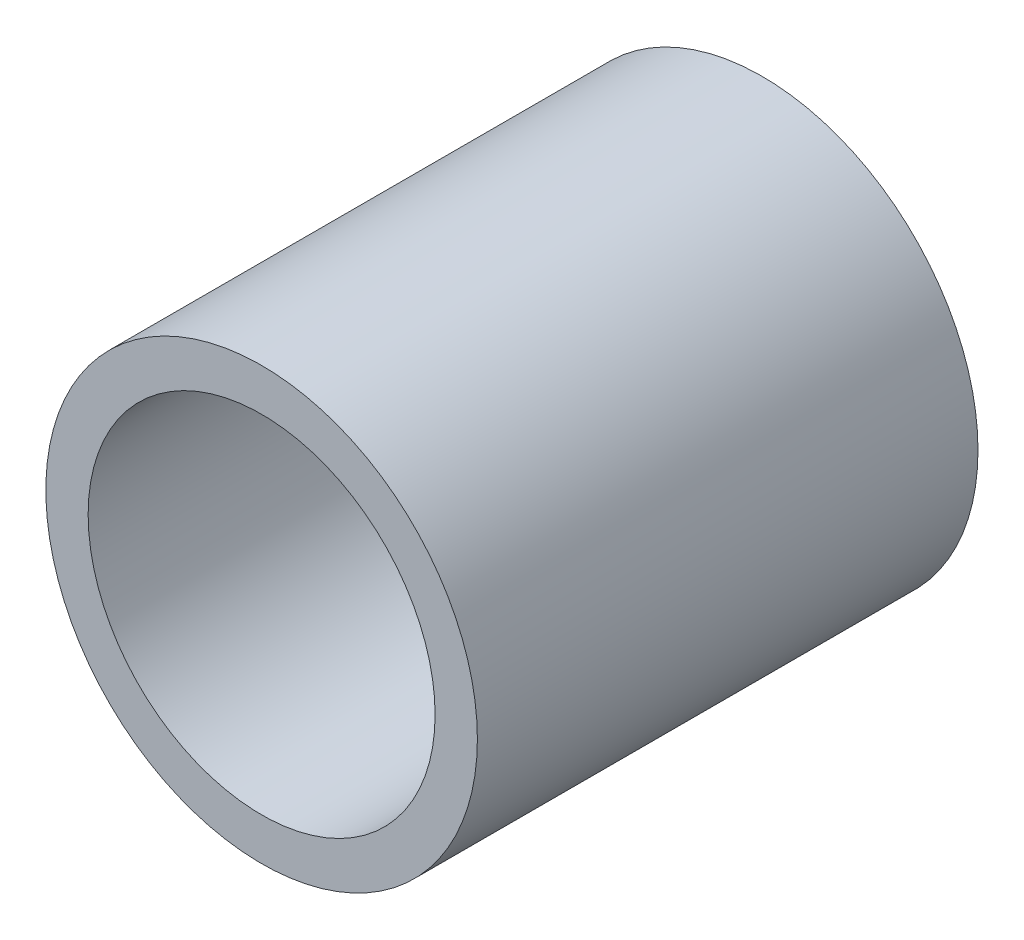
SolidWorks part; units mm, degrees
material "Alloy Steel"
ref_plane "Front Plane" through (0, 0, 0) normal (0, 0, 1) x (1, 0, 0)
ref_plane "Top Plane" through (0, 0, 0) normal (0, 1, 0) x (1, 0, 0)
ref_plane "Right Plane" through (0, 0, 0) normal (1, 0, 0) x (0, 0, -1)
sketch "Sketch1" plane through (0, 0, 0) normal (0, 0, 1) x (1, 0, 0)
  line L0 (-6.35, 0) -> (6.35, 0) construction
  line L1 (0, -6.35) -> (0, 6.35) construction
  circle A0 centre (0, 0) radius 6.35
  circle A1 centre (0, 0) radius 5.1054
  point P4 (0, 0)
  point P9 (0, 0)
  point P10 (5.1054, 0)
  dimension "ID" = 10.2108
  dimension "OD" = 12.7
  dimension "Wall Thickness" = 1.2446
sketch "Sketch2" plane through (0, 0, 0) normal (1, 0, 0) x (0, 0, -1)
  line L0 (7.366, 6.35) -> (-7.366, 6.35) construction
  line L1 (0, 6.35) -> (0, -6.35) construction
  point P3 (7.239, 6.35)
  point P4 (0, 6.35)
  point P5 (-7.239, 6.35)
  dimension "Length" = 14.732
  dimension "D1" = 14.605
  dimension "D2" = 14.605
sketch "Sketch3" plane through (0, 0, 0) normal (0, 0, 1) x (1, 0, 0)
  line L0 (0, -6.35) -> (0, 6.35) construction
  circle A0 centre (0, 0) radius 6.35
  circle A1 centre (0, 0) radius 5.1054
  circle A2 centre (0, 0) radius 5.1054 construction
extrude "Boss-Extrude1" add sketch "Sketch3" along normal mid plane 14.732
equation "\"D1@Boss-Extrude1\" = \"Length@Sketch2\""
equation "\"D1@Sketch2\"=\"OD@Sketch1\"*1.15"
equation "\"D2@Sketch2\"=\"D1@Sketch2\""
